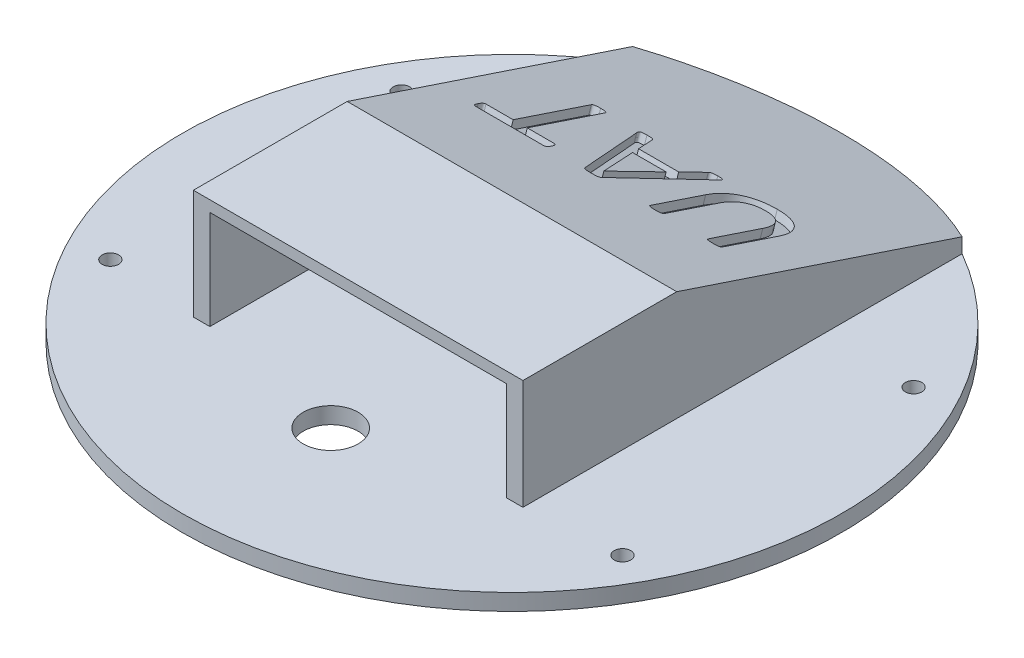
SolidWorks part; units mm, degrees
ref_plane "Front Plane" through (0, 0, 0) normal (0, 0, 1) x (1, 0, 0)
ref_plane "Top Plane" through (0, 0, 0) normal (0, 1, 0) x (1, 0, 0)
ref_plane "Right Plane" through (0, 0, 0) normal (1, 0, 0) x (0, 0, -1)
sketch "Sketch1" plane through (0, 0, 0) normal (0, 1, 0) x (1, 0, 0)
  circle A0 centre (0, 0) radius 60
  dimension "D1" = 120
extrude "Boss-Extrude1" add sketch "Sketch1" along normal blind 3
sketch "Sketch2" plane through (0, 3, 0) normal (0, 1, 0) x (1, 0, 0)
  circle A0 centre (-46.6215, -26.5) radius 1.5 construction
  circle A1 centre (-46.6215, -26.5) radius 1.5
  circle A2 centre (-46.6215, 26.5) radius 1.5 construction
  circle A3 centre (-46.6215, 26.5) radius 1.5
  circle A4 centre (46.6215, 26.5) radius 1.5 construction
  circle A5 centre (46.6215, 26.5) radius 1.5
  circle A6 centre (46.6215, -26.5) radius 1.5 construction
  circle A7 centre (46.6215, -26.5) radius 1.5
extrude "Cut-Extrude1" cut sketch "Sketch2" against normal through all both and the other way through all
sketch "Sketch3" plane through (0, 3, 0) normal (0, 1, 0) x (1, 0, 0)
  line L0 (-27, -28) -> (-27, -3)
  line L1 (-27, -3) -> (27, -3)
  line L2 (27, -3) -> (27, -28)
  line L3 (27, -28) -> (30, -28)
  line L4 (30, -28) -> (30, 0)
  line L5 (30, 0) -> (-30, 0)
  line L6 (-30, 0) -> (-30, -28)
  line L7 (-30, -28) -> (-27, -28)
  point P2 (0, 0)
  point P9 (0, 0)
  point P11 (0, 0)
  dimension "D1" = 3
  dimension "D2" = 3
  dimension "D3" = 3
  dimension "D4" = 54
  dimension "D5" = 25
extrude "Boss-Extrude2" add sketch "Sketch3" along normal blind 18
sketch "Sketch4" plane through (0, 21, 0) normal (0, 1, 0) x (1, 0, 0)
  line L1 (-30, 0) -> (30, 0)
  line L2 (-30, 0) -> (-30, -28)
  line L3 (-30, -28) -> (30, -28)
  line L4 (30, 0) -> (30, -28)
extrude "Boss-Extrude3" add sketch "Sketch4" along normal blind 2
sketch "Sketch5" plane through (0, 3, 0) normal (0, 1, 0) x (1, 0, 0)
  line L0 (-30, -28) -> (30, -28) construction
  circle A0 centre (0, -33) radius 5
  point P4 (0, 0)
  dimension "D1" = 10
  dimension "D2" = 5
extrude "Cut-Extrude2" cut sketch "Sketch5" against normal through all both and the other way through all
sketch "Sketch6" plane through (30, 0, 0) normal (1, 0, 0) x (0, 0, -1)
  line L0 (0, 23) -> (60, 3)
  line L1 (0, 23) -> (0, 3)
  line L2 (0, 3) -> (60, 3)
extrude "Boss-Extrude4" add sketch "Sketch6" against normal up to surface (60 mm away) up to face at (-30, 13, 14)
sketch "Sketch7" plane through (0, 3, 0) normal (0, -1, 0) x (1, 0, 0)
  line L0 (-30, -51.9615) -> (-30, -60) construction
  line L1 (-30, -60) -> (0, -60) construction
  line L2 (0, -60) -> (30, -60) construction
  line L3 (30, -60) -> (30, -51.9615) construction
  line L4 (-30, -51.9615) -> (-30, -60)
  line L5 (-30, -60) -> (0, -60)
  line L6 (0, -60) -> (30, -60)
  line L7 (30, -60) -> (30, -51.9615)
  arc A0 (-30, -51.9615) -> (0, -60) centre (0, 0) ccw construction
  arc A1 (0, -60) -> (30, -51.9615) centre (0, 0) ccw construction
  arc A2 (-30, -51.9615) -> (0, -60) centre (0, 0) ccw
  arc A3 (0, -60) -> (30, -51.9615) centre (0, 0) ccw
extrude "Cut-Extrude3" cut sketch "Sketch7" against normal through all both and the other way through all contours A2 L4 L5
sketch "Sketch8" plane through (0, 20.7, -6.9) normal (0, 0.9487, -0.3162) x (1, 0, 0)
  line L0 (30, 27.499) -> (-30, 27.499) construction
  line L1 (-30, 47.499) -> (30, 47.499) construction
  line L2 (-30, 47.499) -> (-30, -7.2732) construction
  line L3 (-30, -7.2732) -> (30, -7.2732) construction
  line L4 (30, 47.499) -> (30, -7.2732) construction
  text T0 " UAT" font "Calibri" height 17.5
  point P9 (0, 0)
  dimension "D1" = 20
extrude "Cut-Extrude4" cut sketch "Sketch8" against normal blind 1.5
